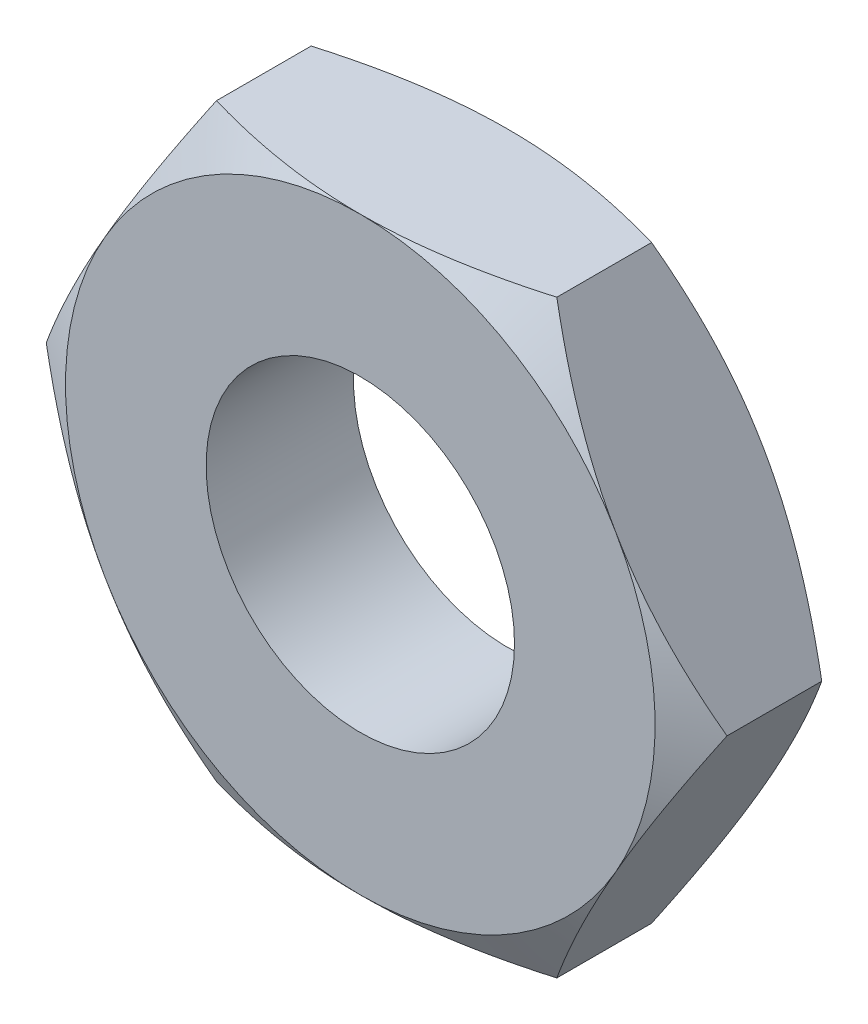
SolidWorks part; units mm, degrees
ref_plane "Front Plane" through (0, 0, 0) normal (0, 0, 1) x (1, 0, 0)
ref_plane "Top Plane" through (0, 0, 0) normal (0, 1, 0) x (1, 0, 0)
ref_plane "Right Plane" through (0, 0, 0) normal (1, 0, 0) x (0, 0, -1)
sketch "Sketch1" plane through (0, 0, 0) normal (0, 0, 1) x (1, 0, 0)
  line L1 (3.7528, -6.5) -> (7.5056, 0)
  line L2 (7.5056, 0) -> (3.7528, 6.5)
  line L3 (3.7528, 6.5) -> (-3.7528, 6.5)
  line L4 (-3.7528, 6.5) -> (-7.5056, 0)
  line L5 (-7.5056, 0) -> (-3.7528, -6.5)
  line L6 (-3.7528, -6.5) -> (3.7528, -6.5)
  circle A0 centre (0, 0) radius 6.5 construction
  dimension "D1" = 13
extrude "Boss-Extrude1" add sketch "Sketch1" along normal blind 3.25
sketch "Sketch3" plane through (0, 0, 0) normal (1, 0, 0) x (0, 0, -1)
  line L0 (0, 0) -> (17.6373, 0) construction
  line L1 (-1.7116, 9.4646) -> (0, 6.5)
  line L3 (0, 6.5) -> (0, 9.4646)
  line L4 (0, 9.4646) -> (-1.7116, 9.4646)
  line L7 (-3.25, 6.5) -> (-3.25, 7.9693)
  line L8 (-3.25, 7.9693) -> (-2.4017, 7.9693)
  line L10 (-3.25, 6.5) -> (-2.4017, 7.9693)
  dimension "D1" = 30
  dimension "D2" = 30
revolve "Cut-Revolve1" cut sketch "Sketch3" angle 360 about L0
hole_wizard "M8 Tapped Hole1" positions "3DSketch1" profile "Sketch4" tap size "M8" standard "ISO" end condition through all
sketch3d "3DSketch1"
  point P0 (0, 0, 3.25)
sketch "Sketch4" plane through (0, 0, 3.25) normal (1, 0, 0) x (0, -1, 0)
  line L0 (0, 0) -> (0, 3.25)
  line L1 (0, 3.25) -> (3.4, 3.25)
  line L2 (3.4, 3.25) -> (3.4, 0)
  line L5 (3.4, 0) -> (0, 0)
  line L11 (0, -6.35) -> (0, 107.95) construction
  dimension "Thru Tap Drill Dia." = 6.8
  dimension "Thru Tap Drill Depth" = 3.25
cosmetic thread "Hole Thread1" parameters "D2"=8
